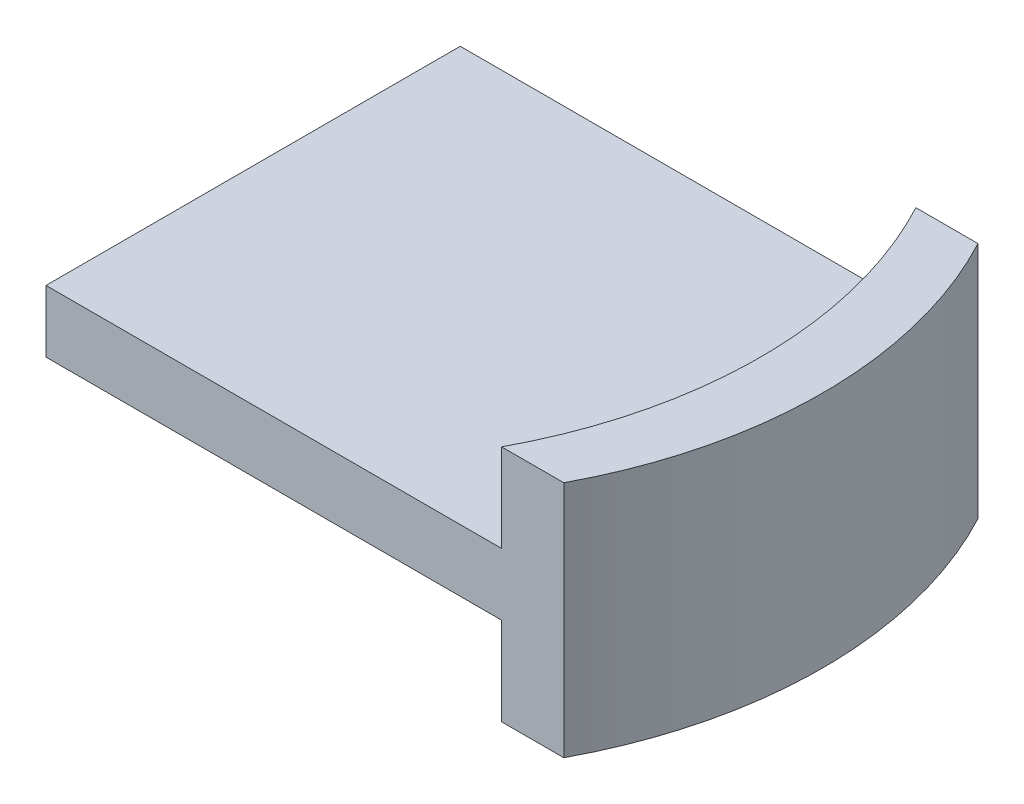
SolidWorks part; units mm, degrees
ref_plane "Front Plane" through (0, 0, 0) normal (0, 0, 1) x (1, 0, 0)
ref_plane "Top Plane" through (0, 0, 0) normal (0, 1, 0) x (1, 0, 0)
ref_plane "Right Plane" through (0, 0, 0) normal (1, 0, 0) x (0, 0, -1)
sketch "Sketch2" plane through (0, 0, 0) normal (0, 1, 0) x (1, 0, 0)
  line L0 (0, 0) -> (-20209.7274, 0) construction
  line L1 (0, 0) -> (0, 20209.7274) construction
  line L2 (0, 4) -> (20209.7274, 4) construction
  line L3 (0, -4) -> (50000, -4) construction
  line L4 (0, 4) -> (1.2, 4)
  line L5 (1.2, -4) -> (0, -4)
  arc A0 (0, 4) -> (0, -4) centre (-7.5, 0) cw
  arc A1 (1.2, 4) -> (1.2, -4) centre (-6.3, 0) cw
  point P12 (1, 0)
  point P19 (2.2, 0)
  dimension "D1" = 4
  dimension "D2" = 4
  dimension "D3" = 1
  dimension "D4" = 1.2
  dimension "D5" = 1.2
  dimension "D6" = 2.2
extrude "Boss-Extrude1" add sketch "Sketch2" along normal mid plane 4.6
sketch "Sketch3" plane through (0, 0, 0) normal (0, 1, 0) x (1, 0, 0)
  line L1 (1.2, 4) -> (-8.8, 4)
  line L2 (1.2, 4) -> (1.2, -4)
  line L3 (1.2, -4) -> (-8.8, -4)
  line L4 (-8.8, 4) -> (-8.8, -4)
  dimension "D1" = 8
  dimension "D2" = 10
extrude "Boss-Extrude2" add sketch "Sketch3" along normal mid plane 1.2
